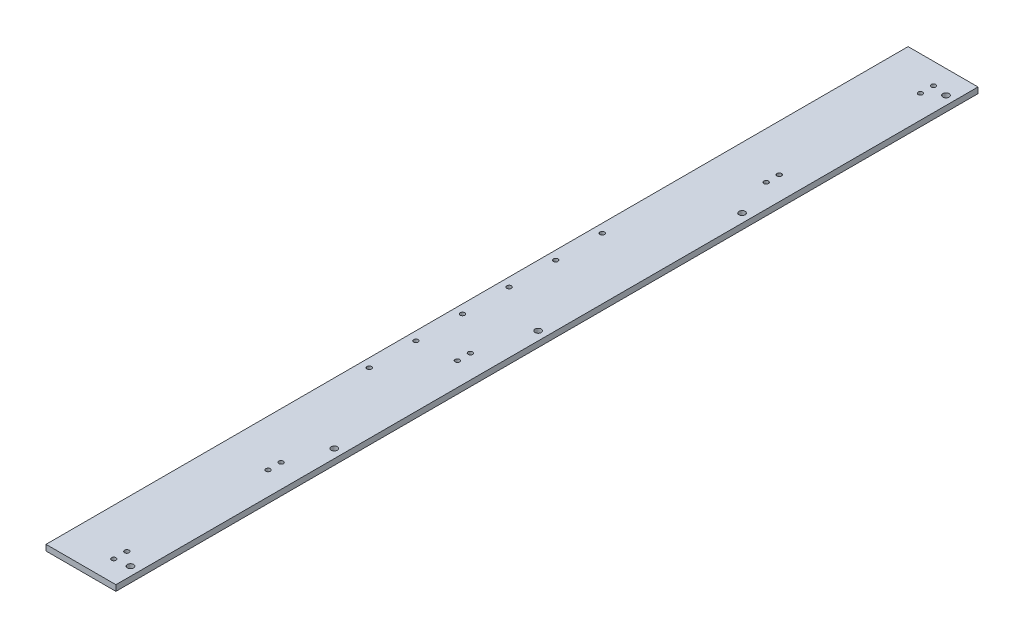
SolidWorks part; units mm, degrees
material "PC High Viscosity"
ref_plane "Front Plane" through (0, 0, 0) normal (0, 0, 1) x (1, 0, 0)
ref_plane "Top Plane" through (0, 0, 0) normal (0, 1, 0) x (1, 0, 0)
ref_plane "Right Plane" through (0, 0, 0) normal (1, 0, 0) x (0, 0, -1)
sketch "Sketch1" plane through (0, 0, 0) normal (0, 0, 1) x (1, 0, 0)
  line L1 (0, 0) -> (76.2, 0)
  line L2 (0, 0) -> (0, 6.35)
  line L3 (0, 6.35) -> (76.2, 6.35)
  line L4 (76.2, 0) -> (76.2, 6.35)
  dimension "D1" = 76.2
  dimension "D2" = 6.35
extrude "Boss-Extrude1" add sketch "Sketch1" along normal blind 939.8
sketch "Sketch2" plane through (0, 6.35, 0) normal (0, 1, 0) x (1, 0, 0)
  line L0 (0, -939.8) -> (0, 0) construction
  circle A0 centre (9.525, -596.9) radius 2.4638
  dimension "D1" = 127
  dimension "D3" = 4.9276
  dimension "D2" = 9.525
extrude "Cut-Extrude1" cut sketch "Sketch2" against normal through all
pattern_linear "LPattern1" count 6 spacing 50.8 along (0, 0, -1) of "Cut-Extrude1"
ref_plane "Plane1" through (0, 0, 469.9) normal (0, 0, 1) x (1, 0, 0)
sketch "Sketch3" plane through (0, 6.35, 0) normal (0, 1, 0) x (1, 0, 0)
  line L0 (76.2, -939.8) -> (0, -939.8) construction
  line L1 (76.2, -939.8) -> (76.2, 0) construction
  circle A0 centre (50.8, -527.939) radius 2.4638
  circle A1 centre (50.8, -542.163) radius 2.4638
  point P6 (0, 0)
  point P9 (0, 0)
  point P11 (66.7861, -535.3349)
  dimension "D1" = 411.861
  dimension "D2" = 4.9276
  dimension "D3" = 25.4
  dimension "D4" = 14.224
extrude "Cut-Extrude2" cut sketch "Sketch3" against normal through all
sketch "Sketch4" plane through (0, 6.35, 0) normal (0, 1, 0) x (1, 0, 0)
  line L0 (76.2, -939.8) -> (76.2, 0) construction
  line L1 (76.2, -939.8) -> (0, -939.8) construction
  circle A0 centre (50.8, -916.686) radius 2.4638
  circle A1 centre (50.8, -902.462) radius 2.4638
  circle A2 centre (50.8, -748.538) radius 2.4638
  circle A3 centre (50.8, -734.314) radius 2.4638
  point P8 (0, 0)
  dimension "D1" = 14.224
  dimension "D3" = 4.9276
  dimension "D2" = 14.224
  dimension "D4" = 25.4
  dimension "D5" = 23.114
  dimension "D6" = 205.486
extrude "Cut-Extrude3" cut sketch "Sketch4" against normal through all
mirror "Mirror1" about plane through (0, 0, 469.9) normal (0, 0, 1) of "Cut-Extrude3"
sketch "Sketch5" plane through (0, 6.35, 0) normal (0, 1, 0) x (1, 0, 0)
  line L0 (-3.4925, -469.9) -> (3.4925, -469.9) construction
  line L1 (76.2, -939.8) -> (76.2, 0) construction
  circle A0 centre (66.675, -469.9) radius 3.3655
  circle A1 centre (66.675, -247.65) radius 3.3655
  circle A2 centre (66.675, -25.4) radius 3.3655
  circle A3 centre (66.675, -692.15) radius 3.3655
  circle A4 centre (66.675, -914.4) radius 3.3655
  point P6 (76.2, -469.9)
  dimension "D1" = 6.731
  dimension "D2" = 9.525
  dimension "D5" = 222.25
  dimension "D6" = 222.25
  dimension "D3" = 3
  dimension "D4" = 3
extrude "Cut-Extrude4" cut sketch "Sketch5" against normal through all and the other way through all
